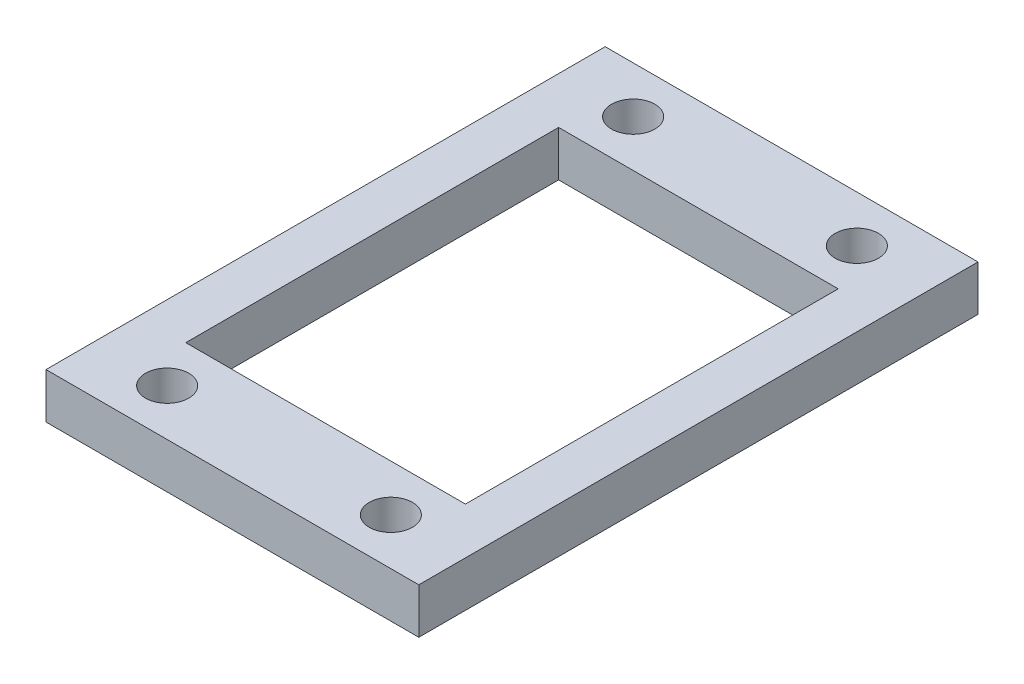
SolidWorks part; units mm, degrees
ref_plane "Front Plane" through (0, 0, 0) normal (0, 0, 1) x (1, 0, 0)
ref_plane "Top Plane" through (0, 0, 0) normal (0, 1, 0) x (1, 0, 0)
ref_plane "Right Plane" through (0, 0, 0) normal (1, 0, 0) x (0, 0, -1)
sketch "Sketch1" plane through (0, 0, 0) normal (0, 1, 0) x (1, 0, 0)
  line L0 (0, 19.05) -> (0, -19.05)
  line L1 (-25.4, 19.05) -> (0, 19.05)
  line L2 (-25.4, 19.05) -> (-25.4, -19.05)
  line L3 (-25.4, -19.05) -> (0, -19.05)
  line L4 (-12.7, 19.05) -> (-12.7, -19.05) construction
  line L5 (-25.4, 0) -> (0, 0) construction
  line L7 (-22.225, -12.7) -> (-3.175, -12.7)
  line L8 (-22.225, -12.7) -> (-22.225, 12.7)
  line L9 (-22.225, 12.7) -> (-3.175, 12.7)
  line L10 (-3.175, -12.7) -> (-3.175, 12.7)
  line L11 (-22.225, -12.7) -> (-3.175, 12.7) construction
  line L12 (-22.225, 12.7) -> (-3.175, -12.7) construction
  circle A0 centre (-5.08, 15.875) radius 1.4732
  circle A1 centre (-20.32, -15.875) radius 1.4732
  circle A2 centre (-20.32, 15.875) radius 1.4732
  circle A3 centre (-5.08, -15.875) radius 1.4732
  point P0 (0, 0)
  point P15 (-12.7, 0)
  dimension "D2" = 25.4
  dimension "D3" = 19.05
  dimension "D4" = 15.875
  dimension "D5" = 2.9464
  dimension "D1" = 7.62
  dimension "D6" = 38.1
  dimension "D7" = 25.4
extrude "Boss-Extrude1" add sketch "Sketch1" along normal blind 3.0988
sketch "Sketch3" plane through (0, 0, 0) normal (0, -1, 0) x (1, 0, 0)
  line L0 (0, 0) -> (-25.4, 0) construction
  line L1 (-25.4, -19.05) -> (-25.4, 19.05) construction
